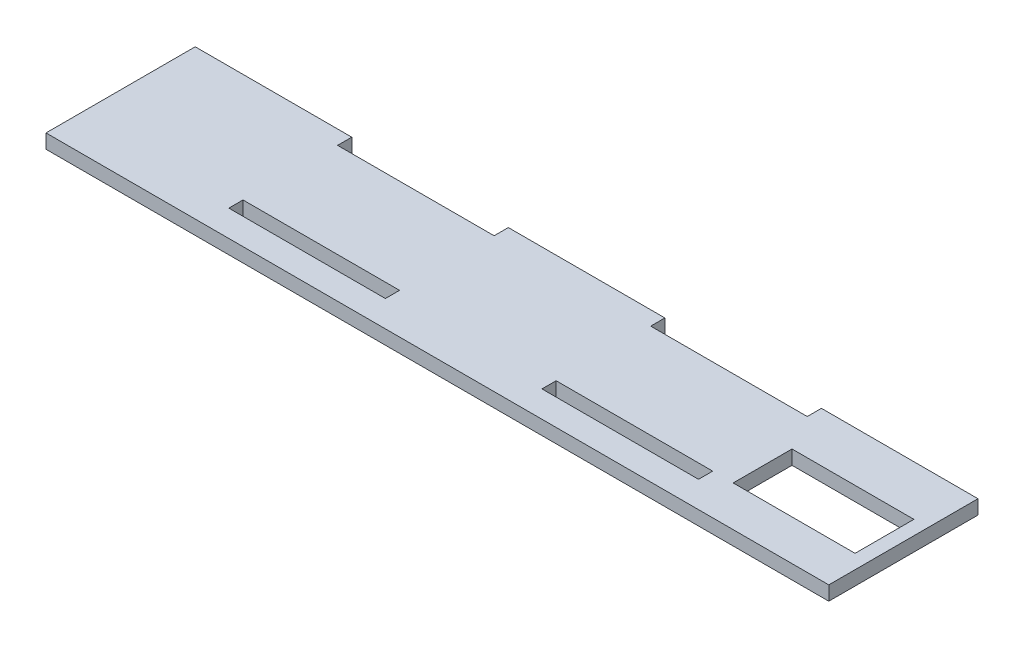
SolidWorks part; units mm, degrees
ref_plane "Front Plane" through (0, 0, 0) normal (0, 0, 1) x (1, 0, 0)
ref_plane "Top Plane" through (0, 0, 0) normal (0, 1, 0) x (1, 0, 0)
ref_plane "Right Plane" through (0, 0, 0) normal (1, 0, 0) x (0, 0, -1)
sketch "Sketch1" plane through (0, 0, 0) normal (0, 1, 0) x (1, 0, 0)
  line L0 (-44.7, -9.2) -> (-14.9, -9.2)
  line L1 (-74.5, -14.2) -> (74.5, -14.2)
  line L2 (-74.5, -14.2) -> (-74.5, 14.2)
  line L3 (-74.5, 14.2) -> (-44.7, 14.2)
  line L4 (74.5, -14.2) -> (74.5, 14.2)
  line L5 (14.9, -9.2) -> (44.7, -9.2)
  line L6 (-44.7, 11.5) -> (-14.9, 11.5)
  line L8 (-14.9, 14.2) -> (14.9, 14.2)
  line L10 (44.7, 14.2) -> (74.5, 14.2)
  line L11 (-44.7, -6.5) -> (-14.9, -6.5)
  line L13 (71.8, -6.5) -> (71.8, 4.7)
  line L14 (14.9, -6.5) -> (44.7, -6.5)
  line L15 (71.8, 4.7) -> (48.6, 4.7)
  line L16 (-44.7, 14.2) -> (-44.7, 11.5)
  line L17 (-14.9, 14.2) -> (-14.9, 11.5)
  line L18 (14.9, 14.2) -> (14.9, 11.5)
  line L19 (44.7, 14.2) -> (44.7, 11.5)
  line L20 (44.7, -6.5) -> (44.7, -9.2)
  line L21 (14.9, -6.5) -> (14.9, -9.2)
  line L22 (-14.9, -6.5) -> (-14.9, -9.2)
  line L23 (-44.7, -6.5) -> (-44.7, -9.2)
  line L24 (48.6, 4.7) -> (48.6, -6.5)
  line L25 (14.9, 11.5) -> (44.7, 11.5)
  line L26 (48.6, -6.5) -> (71.8, -6.5)
  point P0 (0, 0)
  dimension "D1" = 149
  dimension "D2" = 28.4
  dimension "D3" = 5
extrude "Boss-Extrude1" add sketch "Sketch1" along normal blind 2.7
